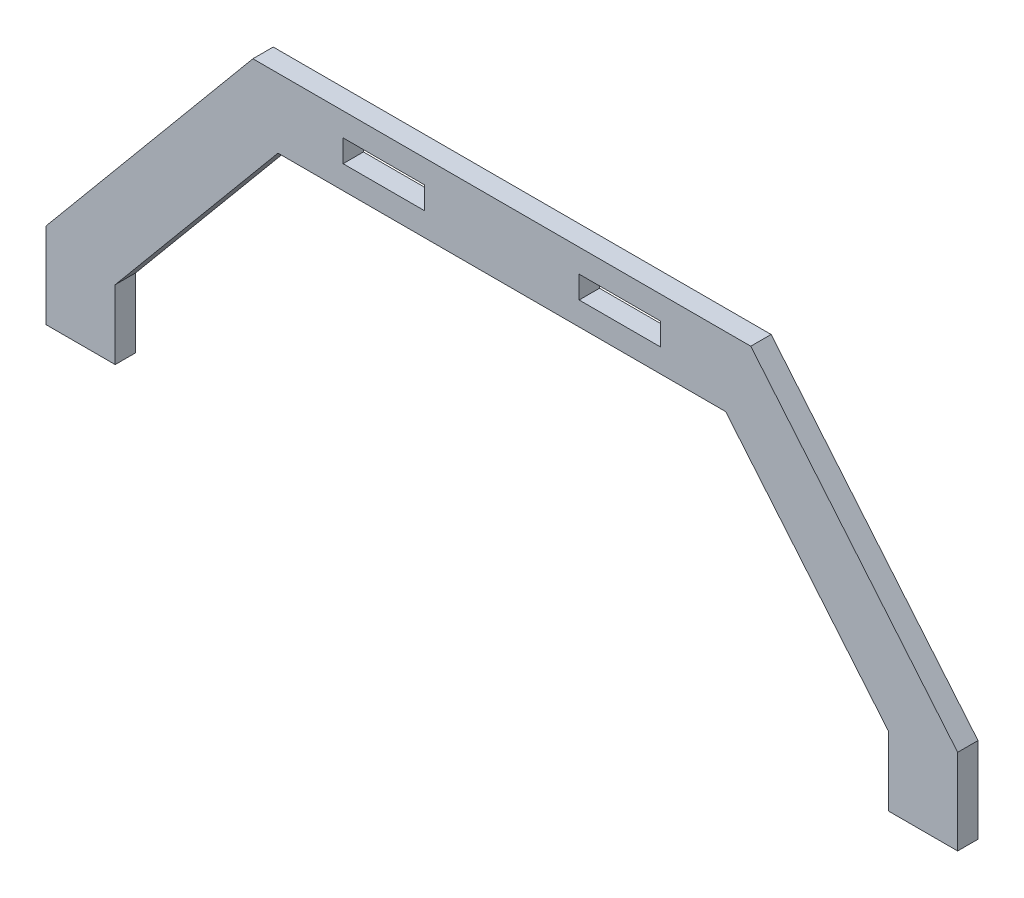
SolidWorks part; units mm, degrees
ref_plane "Plan de face" through (0, 0, 0) normal (0, 0, 1) x (1, 0, 0)
ref_plane "Plan de dessus" through (0, 0, 0) normal (0, 1, 0) x (1, 0, 0)
ref_plane "Plan de droite" through (0, 0, 0) normal (1, 0, 0) x (0, 0, -1)
sketch "Sketch1" plane through (0, 0, 0) normal (0, 0, 1) x (1, 0, 0)
  line L0 (0, 0) -> (0, 82) construction
  line L1 (-112, 0) -> (-95, 0)
  line L2 (-95, 0) -> (-95, 17)
  line L3 (-95, 17) -> (-55, 65)
  line L4 (-55, 65) -> (55, 65)
  line L5 (-112, 0) -> (-112, 21)
  line L6 (-112, 21) -> (-61.1667, 82)
  line L7 (-61.1667, 82) -> (61.1667, 82)
  line L8 (19, 76.25) -> (19, 70.75)
  line L9 (-39, 76.25) -> (-19, 76.25)
  line L10 (-39, 76.25) -> (-39, 70.75)
  line L11 (-39, 70.75) -> (-19, 70.75)
  line L12 (-19, 76.25) -> (-19, 70.75)
  line L13 (39, 70.75) -> (19, 70.75)
  line L14 (39, 76.25) -> (39, 70.75)
  line L15 (39, 76.25) -> (19, 76.25)
  line L16 (112, 21) -> (61.1667, 82)
  line L17 (112, 0) -> (112, 21)
  line L18 (95, 17) -> (55, 65)
  line L19 (95, 0) -> (95, 17)
  line L20 (112, 0) -> (95, 0)
  line L21 (0, 82) -> (0, 65) construction
  line L23 (0, 82) -> (0, 65) construction
  line L25 (0, 65) -> (0, 82) construction
  point P22 (0, 65)
  dimension "D1" = 17
  dimension "D2" = 5.5
  dimension "D3" = 224
  dimension "D4" = 65
  dimension "D5" = 17
  dimension "D6" = 17
  dimension "D7" = 21
  dimension "D8" = 16
  dimension "D9" = 5.75
  dimension "D10" = 20
  dimension "D11" = 40
  dimension "D12" = 19
  dimension "D13" = 122.3333
  dimension "D14" = 110
extrude "Boss-Extrude1" add sketch "Sketch1" along normal blind 5
